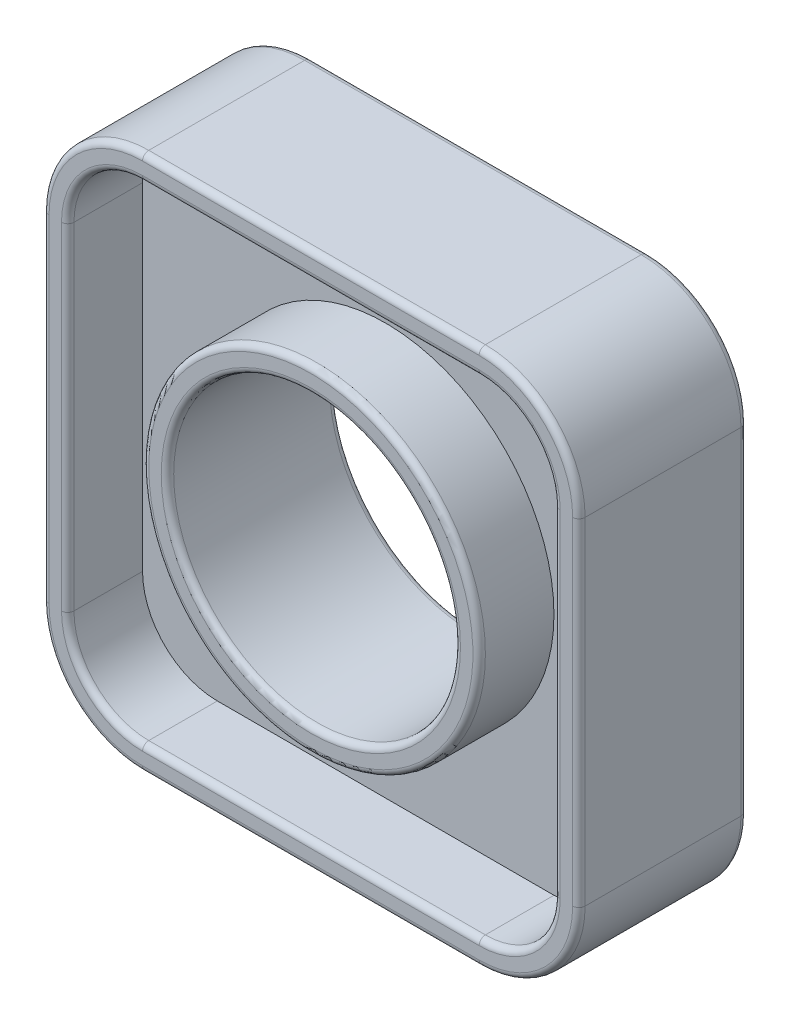
SolidWorks part; units mm, degrees
ref_plane "前基準面" through (0, 0, 0) normal (0, 0, 1) x (1, 0, 0)
ref_plane "上基準面" through (0, 0, 0) normal (0, 1, 0) x (1, 0, 0)
ref_plane "右基準面" through (0, 0, 0) normal (1, 0, 0) x (0, 0, -1)
sketch "草圖1" plane through (0, 0, 0) normal (0, 0, 1) x (1, 0, 0)
  line L1 (-13.5, -21.5) -> (13.5, -21.5)
  line L2 (-21.5, -13.5) -> (-21.5, 13.5)
  line L3 (-13.5, 21.5) -> (13.5, 21.5)
  line L4 (21.5, -13.5) -> (21.5, 13.5)
  line L5 (-21.5, -21.5) -> (21.5, 21.5) construction
  line L6 (-21.5, 21.5) -> (21.5, -21.5) construction
  arc A0 (-13.5, -21.5) -> (-21.5, -13.5) centre (-13.5, -13.5) cw
  arc A1 (13.5, -21.5) -> (21.5, -13.5) centre (13.5, -13.5) ccw
  arc A2 (13.5, 21.5) -> (21.5, 13.5) centre (13.5, 13.5) cw
  arc A3 (-21.5, 13.5) -> (-13.5, 21.5) centre (-13.5, 13.5) cw
  point P0 (0, 0)
  dimension "D3" = 8
  dimension "D1" = 43
  dimension "D2" = 43
extrude "填料-伸長1" add sketch "草圖1" along normal blind 13.5
sketch "草圖2" plane through (0, 0, 13.5) normal (0, 0, 1) x (1, 0, 0)
  line L8 (-13.5, -19.5) -> (13.5, -19.5)
  line L9 (19.5, -13.5) -> (19.5, 13.5)
  line L10 (13.5, 19.5) -> (-13.5, 19.5)
  line L11 (-19.5, 13.5) -> (-19.5, -13.5)
  line L12 (-13.5, -19.5) -> (13.5, -19.5)
  line L13 (19.5, -13.5) -> (19.5, 13.5)
  line L14 (13.5, 19.5) -> (-13.5, 19.5)
  line L15 (-19.5, 13.5) -> (-19.5, -13.5)
  arc A8 (-19.5, -13.5) -> (-13.5, -19.5) centre (-13.5, -13.5) ccw
  arc A9 (13.5, -19.5) -> (19.5, -13.5) centre (13.5, -13.5) ccw
  arc A10 (19.5, 13.5) -> (13.5, 19.5) centre (13.5, 13.5) ccw
  arc A11 (-13.5, 19.5) -> (-19.5, 13.5) centre (-13.5, 13.5) ccw
  arc A12 (-19.5, -13.5) -> (-13.5, -19.5) centre (-13.5, -13.5) ccw
  arc A13 (13.5, -19.5) -> (19.5, -13.5) centre (13.5, -13.5) ccw
  arc A14 (19.5, 13.5) -> (13.5, 19.5) centre (13.5, 13.5) ccw
  arc A15 (-13.5, 19.5) -> (-19.5, 13.5) centre (-13.5, 13.5) ccw
  dimension "D1" = 2
extrude "除料-伸長1" cut sketch "草圖2" against normal blind 6
sketch "草圖3" plane through (0, 0, 0) normal (0, 0, -1) x (-1, 0, 0)
  line L8 (19.5, -13.5) -> (19.5, 13.5)
  line L9 (13.5, 19.5) -> (-13.5, 19.5)
  line L10 (-19.5, 13.5) -> (-19.5, -13.5)
  line L11 (-13.5, -19.5) -> (13.5, -19.5)
  line L12 (19.5, -13.5) -> (19.5, 13.5)
  line L13 (13.5, 19.5) -> (-13.5, 19.5)
  line L14 (-19.5, 13.5) -> (-19.5, -13.5)
  line L15 (-13.5, -19.5) -> (13.5, -19.5)
  arc A8 (13.5, -19.5) -> (19.5, -13.5) centre (13.5, -13.5) ccw
  arc A9 (19.5, 13.5) -> (13.5, 19.5) centre (13.5, 13.5) ccw
  arc A10 (-13.5, 19.5) -> (-19.5, 13.5) centre (-13.5, 13.5) ccw
  arc A11 (-19.5, -13.5) -> (-13.5, -19.5) centre (-13.5, -13.5) ccw
  arc A12 (13.5, -19.5) -> (19.5, -13.5) centre (13.5, -13.5) ccw
  arc A13 (19.5, 13.5) -> (13.5, 19.5) centre (13.5, 13.5) ccw
  arc A14 (-13.5, 19.5) -> (-19.5, 13.5) centre (-13.5, 13.5) ccw
  arc A15 (-19.5, -13.5) -> (-13.5, -19.5) centre (-13.5, -13.5) ccw
  dimension "D1" = 2
extrude "除料-伸長2" cut sketch "草圖3" against normal blind 6
sketch "草圖4" plane through (0, 0, 6) normal (0, 0, -1) x (-1, 0, 0)
  circle A0 centre (0, 0) radius 13.5
  dimension "D1" = 27
extrude "填料-伸長2" add sketch "草圖4" along normal up to surface and the other way up to surface
sketch "草圖5" plane through (0, 0, 13.5) normal (0, 0, 1) x (1, 0, 0)
  circle A0 centre (0, 0) radius 11.5
  dimension "D1" = 23
extrude "除料-伸長3" cut sketch "草圖5" against normal up to next
fillet "圓角1" radius 0.5 36 edges at (-17.7426, -17.7426, 13.5) (-19.5, 0, 13.5) (-17.7426, 17.7426, 13.5) (0, 19.5, 13.5) (17.7426, 17.7426, 13.5) (19.5, 0, 13.5) (17.7426, -17.7426, 13.5) (-19.1569, -19.1569, 13.5) (-21.5, 0, 13.5) (-19.1569, 19.1569, 13.5) (0, 21.5, 13.5) (19.1569, 19.1569, 13.5) (21.5, 0, 13.5) (19.1569, -19.1569, 13.5) (17.7426, -17.7426, 0) (19.5, 0, 0) (17.7426, 17.7426, 0) (0, 19.5, 0) (-17.7426, 17.7426, 0) (-19.5, 0, 0) (-17.7426, -17.7426, 0) (-19.1569, -19.1569, 0) (-21.5, 0, 0) (-19.1569, 19.1569, 0) (0, 21.5, 0) (19.1569, 19.1569, 0) (21.5, 0, 0) (19.1569, -19.1569, 0) (0, -19.5, 13.5) (0, -21.5, 13.5) (0, -19.5, 0) (0, -21.5, 0) (-11.5, 0, 0) (-13.5, 0, 0) (11.5, 0, 13.5) (-13.5, 0, 13.5)
